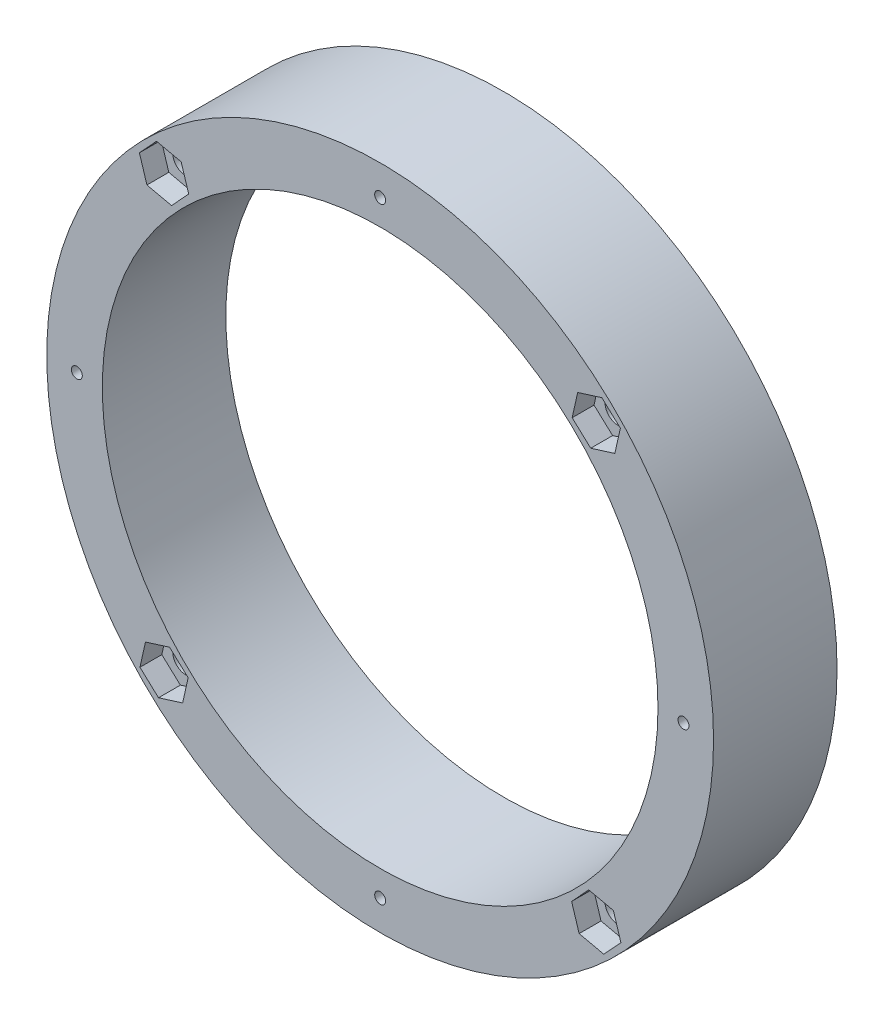
SolidWorks part; units mm, degrees
ref_plane "Front Plane" through (0, 0, 0) normal (0, 0, 1) x (1, 0, 0)
ref_plane "Top Plane" through (0, 0, 0) normal (0, 1, 0) x (1, 0, 0)
ref_plane "Right Plane" through (0, 0, 0) normal (1, 0, 0) x (0, 0, -1)
sketch "Sketch1" plane through (0, 0, 0) normal (0, 0, 1) x (1, 0, 0)
  line L0 (0, 70.5725) -> (0, 76.2) construction
  line L3 (-1.25, 69.3225) -> (12.2983, 69.3225) construction
  circle A0 centre (0, 0) radius 63.5
  circle A1 centre (0, 0) radius 76.2
  circle A2 centre (0, 69.3225) radius 1.25
  circle A3 centre (69.3225, 0) radius 1.25
  circle A4 centre (0, -69.3225) radius 1.25
  circle A5 centre (-69.3225, 0) radius 1.25
  point P19 (0, 0)
  dimension "D1" = 127
  dimension "D2" = 152.4
  dimension "D3" = 2.5
  dimension "D5" = 5.6275
  dimension "D4" = 4
extrude "Boss-Extrude1" add sketch "Sketch1" along normal blind 28.225
sketch "Sketch2" plane through (0, 0, 0) normal (0, 0, -1) x (-1, 0, 0)
  circle A0 centre (0, 69.3225) radius 2.5
  circle A1 centre (69.3225, 0) radius 2.5
  circle A2 centre (0, -69.3225) radius 2.5
  circle A3 centre (-69.3225, 0) radius 2.5
  circle A4 centre (69.3225, 0) radius 1.25 construction
  circle A5 centre (0, -69.3225) radius 1.25 construction
  point P12 (0, 0)
  dimension "D1" = 5
  dimension "D2" = 4
extrude "Cut-Extrude1" cut sketch "Sketch2" against normal blind 6.725
sketch "Sketch3" plane through (0, 0, 28.225) normal (0, 0, 1) x (1, 0, 0)
  line L0 (0, 69.3225) -> (0, 0) construction
  line L1 (0, 0) -> (-79.0122, 79.0122) construction
  line L2 (-53.8815, 53.8815) -> (-53.8815, 44.9013) construction
  line L3 (-53.8815, 44.9013) -> (-44.9013, 44.9013) construction
  line L4 (-53.8815, 44.9013) -> (-46.9345, 51.8484) construction
  circle A0 centre (0, 0) radius 76.2 construction
  circle A1 centre (0, 0) radius 63.5 construction
  circle A2 centre (-49.3914, 49.3914) radius 3
  circle A3 centre (49.3914, 49.3914) radius 3
  circle A4 centre (49.3914, -49.3914) radius 3
  circle A5 centre (-49.3914, -49.3914) radius 3
  point P25 (0, 0)
  dimension "D2" = 6
  dimension "D1" = 45
  dimension "D3" = 4
extrude "Cut-Extrude2" cut sketch "Sketch3" against normal through all
sketch "Sketch4" plane through (0, 0, 28.225) normal (0, 0, 1) x (1, 0, 0)
  line L0 (48.1273, 43.758) -> (53.638, 45.4799)
  line L1 (-43.758, 48.1273) -> (-45.4799, 53.638)
  line L2 (-45.4799, 53.638) -> (-51.1133, 54.9021)
  line L3 (-51.1133, 54.9021) -> (-55.0248, 50.6555)
  line L4 (-55.0248, 50.6555) -> (-53.3029, 45.1448)
  line L5 (-53.3029, 45.1448) -> (-47.6695, 43.8807)
  line L6 (-47.6695, 43.8807) -> (-43.758, 48.1273)
  line L7 (53.638, 45.4799) -> (54.9021, 51.1133)
  line L8 (54.9021, 51.1133) -> (50.6555, 55.0248)
  line L9 (50.6555, 55.0248) -> (45.1448, 53.3029)
  line L10 (45.1448, 53.3029) -> (43.8807, 47.6695)
  line L11 (43.8807, 47.6695) -> (48.1273, 43.758)
  line L12 (43.758, -48.1273) -> (45.4799, -53.638)
  line L13 (45.4799, -53.638) -> (51.1133, -54.9021)
  line L14 (51.1133, -54.9021) -> (55.0248, -50.6555)
  line L15 (55.0248, -50.6555) -> (53.3029, -45.1448)
  line L16 (53.3029, -45.1448) -> (47.6695, -43.8807)
  line L17 (47.6695, -43.8807) -> (43.758, -48.1273)
  line L18 (-48.1273, -43.758) -> (-53.638, -45.4799)
  line L19 (-53.638, -45.4799) -> (-54.9021, -51.1133)
  line L20 (-54.9021, -51.1133) -> (-50.6555, -55.0248)
  line L21 (-50.6555, -55.0248) -> (-45.1448, -53.3029)
  line L22 (-45.1448, -53.3029) -> (-43.8807, -47.6695)
  line L23 (-43.8807, -47.6695) -> (-48.1273, -43.758)
  circle A0 centre (-49.3914, 49.3914) radius 5 construction
  circle A1 centre (49.3914, 49.3914) radius 5 construction
  circle A2 centre (49.3914, -49.3914) radius 5 construction
  circle A3 centre (-49.3914, -49.3914) radius 5 construction
  point P36 (0, 0)
  dimension "D1" = 5.7735
  dimension "D2" = 4
extrude "Cut-Extrude3" cut sketch "Sketch4" against normal blind 5
